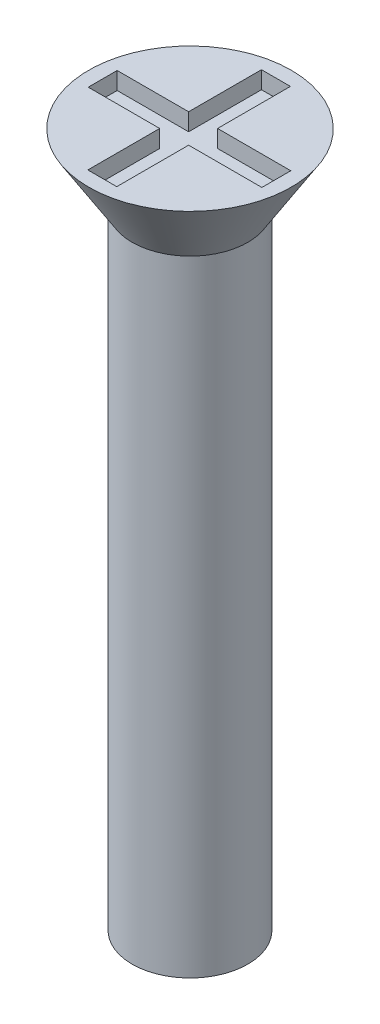
SolidWorks part; units mm, degrees
material "AISI 304"
ref_plane "Front" through (0, 0, 0) normal (0, 0, 1) x (1, 0, 0)
ref_plane "Top" through (0, 0, 0) normal (0, 1, 0) x (1, 0, 0)
ref_plane "Right" through (0, 0, 0) normal (1, 0, 0) x (0, 0, -1)
sketch "Sketch1" plane through (0, 0, 0) normal (0, 1, 0) x (1, 0, 0)
  circle A0 centre (0, 0) radius 1
  dimension "D1" = 2
extrude "Boss-Extrude1" add sketch "Sketch1" along normal blind 12
sketch "Sketch2" plane through (0, 12, 0) normal (0, 1, 0) x (1, 0, 0)
  circle A0 centre (0, 0) radius 1.75
  dimension "D1" = 3.5
extrude "Boss-Extrude2" add sketch "Sketch2" against normal blind 1.3 draft 32
sketch "Sketch3" plane through (0, 12, 0) normal (0, 1, 0) x (1, 0, 0)
  line L1 (-1.5, 0.2416) -> (1.5, 0.2416)
  line L2 (-1.5, 0.2416) -> (-1.5, -0.2584)
  line L3 (-1.5, -0.2584) -> (1.5, -0.2584)
  line L4 (1.5, 0.2416) -> (1.5, -0.2584)
  line L5 (-0.2653, 1.5) -> (0.2347, 1.5)
  line L6 (-0.2653, 1.5) -> (-0.2653, -1.5)
  line L7 (-0.2653, -1.5) -> (0.2347, -1.5)
  line L8 (0.2347, 1.5) -> (0.2347, -1.5)
  circle A0 centre (0, 0) radius 1.75 construction
  dimension "D1" = 0.5
  dimension "D2" = 0.5
  dimension "D3" = 3
  dimension "D4" = 3
  dimension "D5" = 1.5
  dimension "D6" = 1.5
extrude "Cut-Extrude1" cut sketch "Sketch3" against normal blind 0.3 contours L8 L5 L6 L1 | L8 L3 L6 L7 | L6 L1 L2 L3 | L1 L8 L3 L4 | L8 L1 L6 L3
